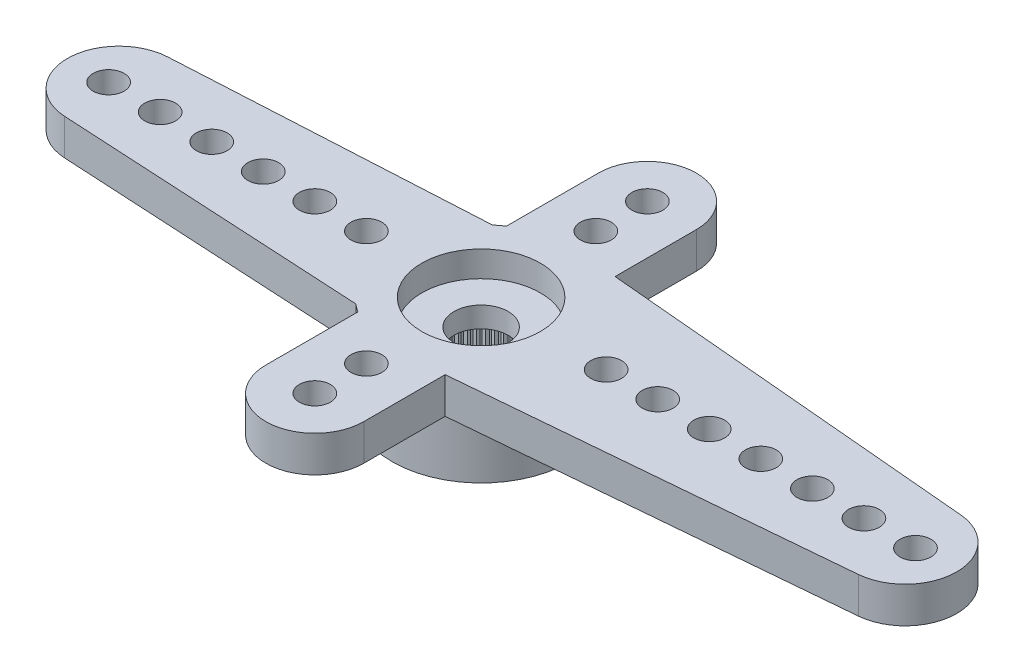
SolidWorks part; units mm, degrees
material "PVC Rígido"
ref_plane "Plano frontal" through (0, 0, 0) normal (0, 0, 1) x (1, 0, 0)
ref_plane "Plano superior" through (0, 0, 0) normal (0, 1, 0) x (1, 0, 0)
ref_plane "Plano direito" through (0, 0, 0) normal (1, 0, 0) x (0, 0, -1)
sketch "Esboço1" plane through (0, 0, 0) normal (0, 1, 0) x (1, 0, 0)
  line L0 (0, 0) -> (-14.05, 0) construction
  line L1 (-14.1591, 1.997) -> (-2.2091, 2.65)
  line L2 (-2.2091, -2.65) -> (-14.1591, -1.997)
  arc A0 (-2.2091, -2.65) -> (-2.2091, 2.65) centre (0, 0) ccw
  arc A1 (-14.1591, 1.997) -> (-14.1591, -1.997) centre (-14.05, 0) ccw
  dimension "D1" = 6.9
  dimension "D2" = 4
  dimension "D3" = 19.5
  dimension "D4" = 5.3
extrude "Ressalto-extrusão1" add sketch "Esboço1" against normal blind 1.4
sketch "Esboço2" plane through (0, -1.4, 0) normal (0, -1, 0) x (1, 0, 0)
  arc A0 (-2.2091, -2.65) -> (-2.2091, 2.65) centre (0, 0) ccw construction
  circle A1 centre (0, 0) radius 3.45
extrude "Ressalto-extrusão2" add sketch "Esboço2" along normal offset from surface (2.4 mm away) 3.8 up to face at (-7.242, 0, 0)
hole_wizard "Furo1" positions "Esboço9" profile "Esboço10" legacy end condition through all
sketch "Esboço9" plane through (0, 0, 0) normal (0, 1, 0) x (1, 0, 0)
  line L1 (-14.45, 0) -> (0, 0) construction
  arc A2 (-14.1591, 1.997) -> (-14.1591, -1.997) centre (-14.05, 0) ccw construction
  point P0 (-14.45, 0)
  point P19 (-16.05, 0)
  dimension "D1" = 1.6
sketch "Esboço10" plane through (-14.45, 0, 0) normal (1, 0, 0) x (0, 0, 1)
  line L0 (0, 0) -> (0, 3.8)
  line L1 (0, 3.8) -> (0.6, 3.8)
  line L2 (0.6, 3.8) -> (0.6, 0)
  line L3 (0.6, 0) -> (0, 0)
  line L4 (0, 110) -> (0, -10) construction
  dimension "Diameter" = 1.2
  dimension "Depth" = 3.8
pattern_linear "Padrão linear1" count 6 spacing 2 along (1, 0, 0) of "Furo1"
sketch "Esboço12" plane through (0, 0, 0) normal (0, 1, 0) x (1, 0, 0)
  line L0 (0.3041, 3.4366) -> (16.6263, 1.9922)
  line L1 (16.6263, -1.9922) -> (0.3041, -3.4366)
  arc A0 (-2.2091, -2.65) -> (-2.2091, 2.65) centre (0, 0) ccw construction
  arc A1 (0.3041, -3.4366) -> (0.3041, 3.4366) centre (0, 0) ccw
  arc A2 (16.6263, 1.9922) -> (16.6263, -1.9922) centre (16.45, 0) cw
  arc A3 (-14.1591, 1.997) -> (-14.1591, -1.997) centre (-14.05, 0) ccw construction
  dimension "D1" = 2
  dimension "D2" = 34.5
extrude "Ressalto-extrusão3" add sketch "Esboço12" against normal up to surface (1.4 mm away) up to face at (-12.45, -1.4, 0.6)
hole_wizard "Furo2" positions "Esboço13" profile "Esboço14" legacy end condition through all
sketch "Esboço13" plane through (0, 0, 0) normal (0, 1, 0) x (1, 0, 0)
  line L0 (0, 0) -> (16.85, 0) construction
  arc A0 (16.6263, -1.9922) -> (16.6263, 1.9922) centre (16.45, 0) ccw construction
  point P0 (16.85, 0)
  point P6 (18.45, 0)
  dimension "D1" = 1.6
sketch "Esboço14" plane through (16.85, 0, 0) normal (1, 0, 0) x (0, 0, 1)
  line L0 (0, 0) -> (0, 3.8)
  line L1 (0, 3.8) -> (0.6, 3.8)
  line L2 (0.6, 3.8) -> (0.6, 0)
  line L3 (0.6, 0) -> (0, 0)
  line L4 (0, 110) -> (0, -10) construction
  dimension "Diameter" = 1.2
  dimension "Depth" = 3.8
pattern_linear "Padrão linear2" count 7 spacing 2 along (-1, 0, 0) of "Furo2"
sketch "Esboço16" plane through (0, 0, 0) normal (0, 1, 0) x (1, 0, 0)
  line L0 (0, -6.45) -> (0, 6.45) construction
  line L1 (-1.9, -6.45) -> (-1.9, 6.45)
  line L2 (1.9, -6.45) -> (1.9, 6.45)
  arc A0 (-1.9, -6.45) -> (1.9, -6.45) centre (0, -6.45) ccw
  arc A1 (1.9, 6.45) -> (-1.9, 6.45) centre (0, 6.45) ccw
  point P2 (0, 0)
  dimension "D2" = 16.7
  dimension "D1" = 3.8
extrude "Ressalto-extrusão4" add sketch "Esboço16" against normal up to surface (1.4 mm away) up to face at (14.85, -1.4, 0.6)
hole_wizard "Furo3" positions "Esboço17" profile "Esboço18" legacy end condition through all
sketch "Esboço17" plane through (0, 0, 0) normal (0, 1, 0) x (1, 0, 0)
  point P0 (0, -6.45)
sketch "Esboço18" plane through (0, 0, 6.45) normal (1, 0, 0) x (0, 0, 1)
  line L0 (0, 0) -> (0, 3.8)
  line L1 (0, 3.8) -> (0.6, 3.8)
  line L2 (0.6, 3.8) -> (0.6, 0)
  line L3 (0.6, 0) -> (0, 0)
  line L4 (0, 110) -> (0, -10) construction
  dimension "Diameter" = 1.2
  dimension "Depth" = 3.8
pattern_linear "Padrão linear3" count 2 spacing 2 along (0, 0, -1) of "Furo3"
pattern_circular "PadrãoCircular1" count 2 over 360 about axis through (0, 0, 0) along (0, 1, 0) of "Padrão linear3", "Furo3"
hole_wizard "Furo4" positions "Esboço3" profile "Esboço4" legacy
sketch "Esboço3" plane through (0, -3.8, 0) normal (0, -1, 0) x (-1, 0, 0)
  point P0 (0, 0)
sketch "Esboço4" plane through (0, -3.8, 0) normal (1, 0, 0) x (0, 0, -1)
  line L0 (0, 0) -> (0, 2)
  line L1 (0, 2) -> (2.475, 2)
  line L2 (2.475, 2) -> (2.475, 0)
  line L3 (2.475, 0) -> (0, 0)
  line L4 (0, 110) -> (0, -10) construction
  dimension "Diameter" = 4.95
  dimension "Depth" = 2
hole_wizard "Furo5" positions "Esboço5" profile "Esboço6" legacy
sketch "Esboço5" plane through (0, 0, 0) normal (0, 1, 0) x (1, 0, 0)
  point P0 (0, 0)
sketch "Esboço6" plane through (0, 0, 0) normal (1, 0, 0) x (0, 0, 1)
  line L0 (0, 0) -> (0, 1)
  line L1 (0, 1) -> (2.3, 1)
  line L2 (2.3, 1) -> (2.3, 0)
  line L3 (2.3, 0) -> (0, 0)
  line L4 (0, 110) -> (0, -10) construction
  dimension "Diameter" = 4.6
  dimension "Depth" = 1
hole_wizard "Furo6" positions "Esboço7" profile "Esboço8" legacy end condition through all
sketch "Esboço7" plane through (0, 0, 0) normal (0, 1, 0) x (1, 0, 0)
  point P0 (0, 0)
sketch "Esboço8" plane through (0, 0, 0) normal (1, 0, 0) x (0, 0, 1)
  line L0 (0, 0) -> (0, 3.8)
  line L1 (0, 3.8) -> (1.05, 3.8)
  line L2 (1.05, 3.8) -> (1.05, 0)
  line L3 (1.05, 0) -> (0, 0)
  line L4 (0, 110) -> (0, -10) construction
  dimension "Diameter" = 2.1
  dimension "Depth" = 3.8
sketch "Esboço11" plane through (0, -3.8, 0) normal (0, -1, 0) x (1, 0, 0)
  line L0 (-0.0981, 2.4731) -> (0, 2.375)
  line L1 (0, 2.375) -> (0.0981, 2.4731)
  line L2 (0, 0) -> (0, 2.475) construction
  circle A0 centre (0, 0) radius 2.375 construction
  circle A1 centre (0, 0) radius 2.475
  arc A2 (0.0981, 2.4731) -> (-0.0981, 2.4731) centre (0, 0) ccw
  dimension "D3" = 4.75
  dimension "D2" = 0.1
  dimension "D1" = 0
extrude "Ressalto-extrusão5" add sketch "Esboço11" against normal up to surface (2 mm away) up to face at (0, -1.8, 1.05)
pattern_circular "PadrãoCircular2" count 60 over 360 about axis through (0, 0, 0) along (0, 1, 0) of "Ressalto-extrusão5"
sketch "Sketch1" plane through (0, 0, 0) normal (0, 1, 0) x (1, 0, 0)
  line L0 (-8.45, 0) -> (8.85, 0) construction
  line L1 (0, 2.617) -> (4.85, 2.617) construction
  line L2 (4.85, 2.007) -> (6.85, 2.007) construction
  line L3 (4.25, 0) -> (4.25, 1.7064) construction
  line L4 (2.3, 0) -> (2.3, 1.7064) construction
  line L5 (2.3, 1.7064) -> (4.25, 1.7064) construction
  line L6 (6.25, 0) -> (6.25, 1.7064) construction
  line L7 (5.45, 0) -> (5.45, 1.7064) construction
  line L8 (5.45, 1.7064) -> (6.25, 1.7064) construction
  circle A0 centre (0, 0) radius 1.05
  circle A1 centre (0, 0) radius 2.3
  circle A2 centre (4.85, 0) radius 0.6
  circle A3 centre (6.85, 0) radius 0.6
  circle A4 centre (8.85, 0) radius 0.6
  circle A5 centre (-4.45, 0) radius 0.6
  circle A6 centre (-6.45, 0) radius 0.6
  circle A7 centre (-8.45, 0) radius 0.6
  dimension "D1" = 4.6
  dimension "D2" = 1.2
  dimension "D3" = 2.1
  dimension "D4" = 0.8
sketch "Sketch2" plane through (-1.9, 0, 0) normal (-1, 0, 0) x (0, 0, 1)
  line L0 (2.8797, 0) -> (2.8797, -3.8015)
